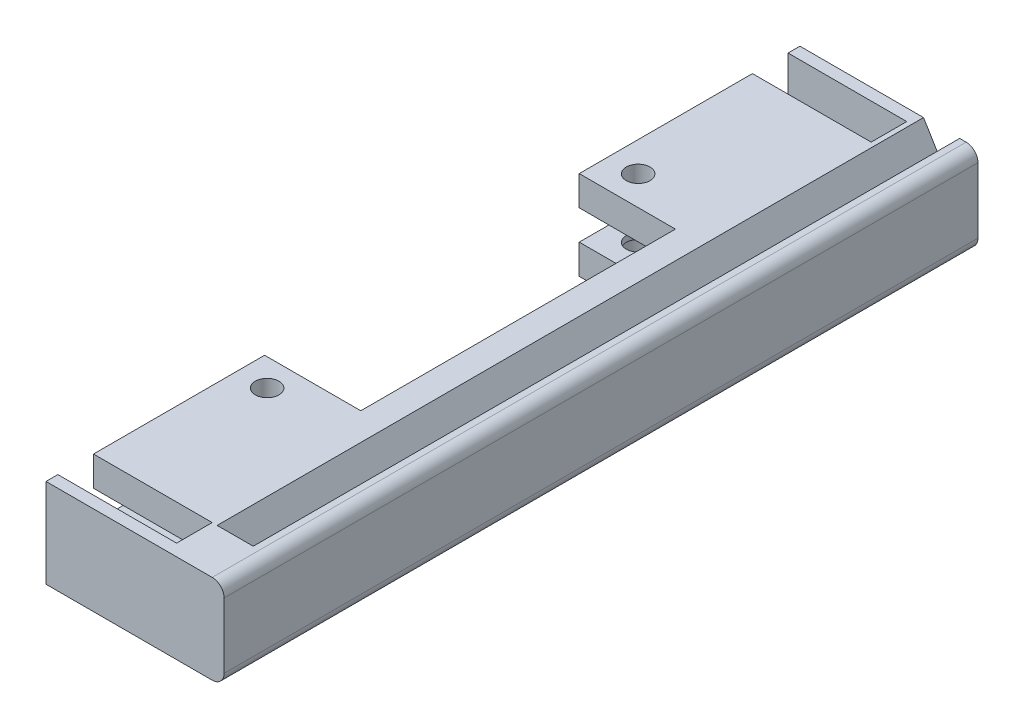
SolidWorks part; units mm, degrees
ref_plane "Alzado" through (0, 0, 0) normal (0, 0, 1) x (1, 0, 0)
ref_plane "Planta" through (0, 0, 0) normal (0, 1, 0) x (1, 0, 0)
ref_plane "Vista lateral" through (0, 0, 0) normal (1, 0, 0) x (0, 0, -1)
sketch "Croquis1" plane through (0, 0, 0) normal (0, 0, 1) x (1, 0, 0)
  line L0 (0, 0) -> (0, 15)
  line L1 (0, 15) -> (28, 15)
  line L2 (0, 0) -> (28, 0)
  line L3 (30, 13) -> (30, 2)
  line L4 (0, 7.5) -> (30, 7.5) construction
  line L6 (0, 10) -> (20, 10)
  line L7 (0, 10) -> (0, 5)
  line L8 (0, 5) -> (20, 5)
  line L9 (20, 10) -> (20, 5)
  arc A0 (28, 0) -> (30, 2) centre (28, 2) ccw
  arc A1 (28, 15) -> (30, 13) centre (28, 13) cw
  point P7 (30, 0)
  dimension "D3" = 2
  dimension "D1" = 15
  dimension "D2" = 30
  dimension "D4" = 20
  dimension "D5" = 5
  dimension "D6" = 5
extrude "Saliente-Extruir1" add sketch "Croquis1" along normal blind 111 contours L4 L9 L8 L0 L2 A0 L3 | L9 L4 L3 A1 L1 L0 L6
sketch "Croquis2" plane through (0, 0, 111) normal (0, 0, 1) x (1, 0, 0)
  line L0 (20, 10) -> (20, 15)
  line L8 (30, 2) -> (30, 13)
  line L9 (28, 15) -> (0, 15)
  line L10 (0, 15) -> (0, 10)
  line L11 (0, 10) -> (20, 10)
  line L12 (20, 10) -> (20, 5)
  line L13 (20, 5) -> (0, 5)
  line L14 (0, 5) -> (0, 0)
  line L15 (0, 0) -> (28, 0)
  line L16 (30, 2) -> (30, 13)
  line L17 (28, 15) -> (0, 15)
  line L18 (0, 15) -> (0, 10)
  line L19 (0, 10) -> (20, 10)
  line L20 (20, 10) -> (20, 5)
  line L21 (20, 5) -> (0, 5)
  line L22 (0, 5) -> (0, 0)
  line L23 (0, 0) -> (28, 0)
  arc A2 (30, 13) -> (28, 15) centre (28, 13) ccw
  arc A3 (28, 0) -> (30, 2) centre (28, 2) ccw
  arc A4 (30, 13) -> (28, 15) centre (28, 13) ccw
  arc A5 (28, 0) -> (30, 2) centre (28, 2) ccw
  line M11 (30, 2) -> (30, 13)
  arc M12 (30, 13) -> (28, 15) centre (28, 13) ccw
  line M13 (28, 15) -> (0, 15)
  line M16 (20, 10) -> (20, 5)
  line M17 (20, 5) -> (0, 5)
  line M18 (0, 5) -> (0, 0)
  line M19 (0, 0) -> (28, 0)
  arc M20 (28, 0) -> (30, 2) centre (28, 2) ccw
  dimension "D1" = 0
extrude "Saliente-Extruir2" add sketch "Croquis2" along normal blind 6 contours L0 M16 M17 M18 M19 M20 M11 M12 M13
sketch "Croquis3" plane through (0, 0, 117) normal (0, 0, 1) x (1, 0, 0)
  line L0 (20, 15) -> (20, 5) construction
  line L1 (20, 5) -> (0, 5) construction
  line L2 (0, 5) -> (0, 0) construction
  line L3 (0, 0) -> (28, 0) construction
  line L6 (0, 10) -> (20, 10) construction
  line L7 (20, 10) -> (20, 15) construction
  line L8 (20, 15) -> (0, 15) construction
  line L9 (0, 15) -> (0, 10) construction
  line L10 (20, 15) -> (20, 5)
  line L11 (20, 5) -> (0, 5)
  line L12 (0, 5) -> (0, 0)
  line L13 (0, 0) -> (28, 0)
  line L15 (11, 15) -> (20, 15)
  line L16 (0, 10) -> (20, 10)
  line L17 (20, 10) -> (20, 15)
  line L18 (20, 15) -> (0, 15)
  line L19 (0, 15) -> (0, 10)
  line L20 (0, 10) -> (0, 5)
  line L26 (20, 15) -> (20, 5)
  line L27 (20, 5) -> (0, 5)
  line L28 (0, 5) -> (0, 0)
  line L29 (0, 0) -> (28, 0)
  line L30 (30, 2) -> (30, 13)
  line L31 (20, 15) -> (20, 5)
  line L32 (20, 5) -> (0, 5)
  line L33 (0, 5) -> (0, 0)
  line L34 (0, 0) -> (28, 0)
  line L35 (30, 2) -> (30, 13)
  line L37 (28, 15) -> (20, 15)
  line L38 (28, 15) -> (20, 15)
  arc A6 (28, 0) -> (30, 2) centre (28, 2) ccw
  arc A7 (30, 13) -> (28, 15) centre (28, 13) ccw
  arc A8 (28, 0) -> (30, 2) centre (28, 2) ccw
  arc A9 (30, 13) -> (28, 15) centre (28, 13) ccw
  line M1 (20, 15) -> (20, 5)
  line M2 (20, 5) -> (0, 5)
  line M3 (0, 5) -> (0, 0)
  line M4 (0, 0) -> (28, 0)
  arc M5 (28, 0) -> (30, 2) centre (28, 2) ccw
  line M6 (30, 2) -> (30, 13)
  arc M7 (30, 13) -> (28, 15) centre (28, 13) ccw
  line M8 (28, 15) -> (20, 15)
  dimension "D1" = 0
extrude "Saliente-Extruir3" add sketch "Croquis3" along normal blind 2 contours L18 L19 L16 M1 | L10 M8 M1 M2 M3 M4 M5 M6 M7 | L16 L20 L10 M2
sketch "Croquis4" plane through (0, 0, 0) normal (0, 0, -1) x (-1, 0, 0)
  line L0 (-20, 10) -> (-20, 15)
  line L8 (-30, 13) -> (-30, 2)
  line L9 (-28, 0) -> (0, 0)
  line L10 (0, 0) -> (0, 5)
  line L11 (0, 5) -> (-20, 5)
  line L12 (-20, 5) -> (-20, 10)
  line L13 (-20, 10) -> (0, 10)
  line L14 (0, 10) -> (0, 15)
  line L15 (0, 15) -> (-28, 15)
  line L16 (-30, 13) -> (-30, 2)
  line L17 (-28, 0) -> (0, 0)
  line L18 (0, 0) -> (0, 5)
  line L19 (0, 5) -> (-20, 5)
  line L20 (-20, 5) -> (-20, 10)
  line L21 (-20, 10) -> (0, 10)
  line L22 (0, 10) -> (0, 15)
  line L23 (0, 15) -> (-28, 15)
  arc A2 (-30, 2) -> (-28, 0) centre (-28, 2) ccw
  arc A3 (-28, 15) -> (-30, 13) centre (-28, 13) ccw
  arc A4 (-30, 2) -> (-28, 0) centre (-28, 2) ccw
  arc A5 (-28, 15) -> (-30, 13) centre (-28, 13) ccw
  line M11 (-30, 13) -> (-30, 2)
  arc M12 (-30, 2) -> (-28, 0) centre (-28, 2) ccw
  line M13 (-28, 0) -> (0, 0)
  line M14 (0, 0) -> (0, 5)
  line M15 (0, 5) -> (-20, 5)
  line M16 (-20, 5) -> (-20, 10)
  line M19 (0, 15) -> (-28, 15)
  arc M20 (-28, 15) -> (-30, 13) centre (-28, 13) ccw
  dimension "D1" = 0
extrude "Saliente-Extruir4" add sketch "Croquis4" along normal blind 6 contours L0 M16 M19 M20 M11 M12 M13 M14 M15
sketch "Croquis5" plane through (0, 0, -6) normal (0, 0, -1) x (-1, 0, 0)
  line L3 (0, 15) -> (-20, 15) construction
  line L7 (0, 15) -> (-20, 15) construction
  line L17 (0, 15) -> (-11, 15)
  line L21 (0, 15) -> (-11, 15)
  line L30 (-28, 0) -> (0, 0) construction
  line L31 (0, 0) -> (0, 5) construction
  line L35 (0, 5) -> (0, 15) construction
  line L38 (0, 10) -> (0, 15) construction
  line L41 (-28, 0) -> (0, 0)
  line L42 (0, 0) -> (0, 5)
  line L46 (0, 5) -> (0, 15)
  line L47 (0, 15) -> (-20, 15)
  line L50 (0, 10) -> (0, 15)
  line L51 (0, 15) -> (-20, 15)
  line L52 (0, 10) -> (0, 5)
  line L53 (-20, 15) -> (-20, 5) construction
  line L54 (-20, 5) -> (0, 5) construction
  line L55 (0, 5) -> (0, 15) construction
  line L56 (0, 15) -> (-20, 15) construction
  line L57 (-20, 15) -> (-20, 10) construction
  line L58 (-20, 10) -> (0, 10) construction
  line L59 (-20, 5) -> (-20, 15) construction
  line L60 (-20, 15) -> (-28, 15) construction
  line L61 (-30, 13) -> (-30, 2) construction
  line L62 (0, 5) -> (-20, 5) construction
  line L63 (-20, 15) -> (-20, 5)
  line L64 (-20, 5) -> (0, 5)
  line L65 (0, 5) -> (0, 15)
  line L66 (0, 15) -> (-20, 15)
  line L67 (-20, 15) -> (-20, 10)
  line L68 (-20, 10) -> (0, 10)
  line L69 (0, 10) -> (0, 15)
  line L70 (0, 15) -> (-20, 15)
  line L71 (-20, 5) -> (-20, 15)
  line L72 (-20, 15) -> (-28, 15)
  line L73 (-30, 13) -> (-30, 2)
  line L74 (-28, 0) -> (0, 0)
  line L75 (0, 0) -> (0, 5)
  line L76 (0, 5) -> (-20, 5)
  arc A8 (-28, 15) -> (-30, 13) centre (-28, 13) ccw construction
  arc A9 (-30, 2) -> (-28, 0) centre (-28, 2) ccw construction
  arc A10 (-28, 15) -> (-30, 13) centre (-28, 13) ccw
  arc A11 (-30, 2) -> (-28, 0) centre (-28, 2) ccw
extrude "Saliente-Extruir5" add sketch "Croquis5" along normal blind 2
sketch "Croquis6" plane through (0, 0, 0) normal (0, -1, 0) x (1, 0, 0)
  line L0 (5, -7) -> (5, 118) construction
  line L3 (0, 119) -> (0, -8) construction
  circle A0 centre (5, 24.25) radius 2
  circle A1 centre (5, 86.75) radius 2
  point P10 (5, 55.5)
  dimension "D1" = 4
  dimension "D2" = 4
  dimension "D3" = 31.25
  dimension "D4" = 31.25
  dimension "D5" = 5
extrude "Cortar-Extruir1" cut sketch "Croquis6" against normal blind 41
sketch "Croquis7" plane through (0, 0, 0) normal (0, -1, 0) x (-1, 0, 0)
  circle A0 centre (-5, -24.25) radius 4
  circle A1 centre (-5, -86.75) radius 4
  dimension "D1" = 8
  dimension "D2" = 8
extrude "Cortar-Extruir2" cut sketch "Croquis7" against normal blind 4
sketch "Croquis8" plane through (0, 15, 0) normal (0, 1, 0) x (1, 0, 0)
  line L0 (0, 6) -> (20, 6) construction
  line L1 (22, 6) -> (28, 6)
  line L2 (22, 6) -> (22, 0)
  line L3 (22, 0) -> (28, 0)
  line L4 (28, 6) -> (28, 0)
  line L5 (28, -119) -> (28, 8) construction
  line L6 (0, -111) -> (20, -111) construction
  line L7 (22, -111) -> (28, -111)
  line L8 (22, -111) -> (22, -116.1119)
  line L9 (22, -116.1119) -> (28, -116.1119)
  line L10 (28, -111) -> (28, -116.1119)
  dimension "D1" = 6
  dimension "D2" = 5.1119
  dimension "D3" = 6
extrude "Cortar-Extruir3" [suppressed] cut sketch "Croquis8" against normal blind 5
sketch "Croquis9" plane through (0, 0, 0) normal (0, -1, 0) x (1, 0, 0)
  line L0 (0, 119) -> (0, -8) construction
  line L1 (0, 29.1749) -> (16.2, 29.1749)
  line L2 (0, 29.1749) -> (0, 82.1749)
  line L3 (0, 82.1749) -> (16.2, 82.1749)
  line L4 (16.2, 29.1749) -> (16.2, 82.1749)
  line L5 (28, 119) -> (28, -8) construction
  dimension "D1" = 53
  dimension "D2" = 11.8
extrude "Cortar-Extruir4" cut sketch "Croquis9" against normal blind 20
sketch "Croquis10" plane through (0, 0, -8) normal (0, 0, -1) x (-1, 0, 0)
  line L0 (-26.9106, 15) -> (-28.4201, 12.5067)
  line L1 (0, 15) -> (-28, 15) construction
  line L2 (-28.4201, 12.5067) -> (-23.9093, 9.9094)
  line L3 (-23.9093, 9.9094) -> (-20.8274, 15)
  line L4 (-20.8274, 15) -> (-26.9106, 15)
  point P4 (-26.7943, 15)
  point P7 (-27.8716, 11.341)
  point P8 (-28.0478, 11.4193)
  point P9 (-23.7192, 9.7153)
  point P10 (0, 0)
  point P11 (-28.4787, 11.576)
  point P12 (-21.1005, 15)
  point P13 (-26.967, 15)
  point P14 (-23.6389, 9.7615)
  point P15 (-21.1005, 15)
  point P16 (-27.5029, 15)
  point P17 (-22.4825, 15)
  point P18 (-23.6389, 9.7333)
  point P19 (-28.4901, 12.1025)
  point P20 (-24.203, 10.1282)
  point P21 (-24.2876, 10.5795)
  point P22 (-28, 15)
  point P24 (-23.3851, 10.9461)
  point P25 (-28, 15)
  point P26 (-28, 15)
  point P27 (-28, 15)
  point P28 (-27.3337, 15)
  point P29 (-26.9106, 15)
  point P30 (-24.1184, 9.5641)
extrude "Cortar-Extruir5" cut sketch "Croquis10" against normal up to surface (119 mm away) up to face at (10, 12.5, 111)
